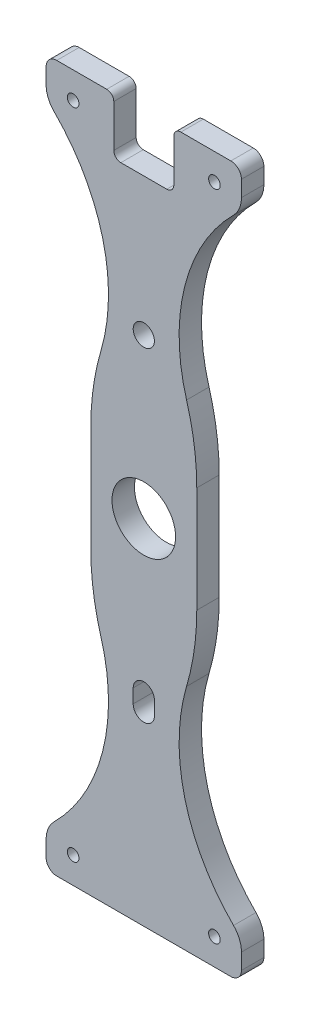
SolidWorks part; units mm, degrees
material "6061-T6 (SS)"
ref_plane "Front Plane" through (0, 0, 0) normal (0, 0, 1) x (1, 0, 0)
ref_plane "Top Plane" through (0, 0, 0) normal (0, 1, 0) x (1, 0, 0)
ref_plane "Right Plane" through (0, 0, 0) normal (1, 0, 0) x (0, 0, -1)
sketch "Sketch1" plane through (0, 0, 0) normal (0, 0, 1) x (1, 0, 0)
  line L5 (-15, 0) -> (15, 0) construction
  line L6 (0, -43.0352) -> (0, -46.957) construction
  line L10 (3, -43.0352) -> (3, -46.957)
  line L13 (240, 100) -> (240, -100) construction
  line L14 (-3, -43.0352) -> (-3, -46.957)
  line L15 (-15, 15) -> (-15, -15)
  line L18 (-24.65, -100) -> (24.65, -100)
  line L21 (15, -15) -> (15, 15)
  line L23 (27.65, 92.5) -> (27.65, 97)
  line L24 (24.65, 100) -> (-24.65, 100)
  line L25 (-27.65, 97) -> (-27.65, 92.5)
  line L27 (27.65, -92.5) -> (27.65, -97)
  line L28 (-27.65, -97) -> (-27.65, -92.5)
  line L29 (-3.92, 79.4898) -> (-3.92, -120.5102) construction
  line L30 (0, 100) -> (0, 0) construction
  line L31 (-10, -49.8891) -> (-10, -92.5) construction
  line L32 (-10, -92.5) -> (10, -92.5) construction
  line L33 (10, -92.5) -> (10, -49.8891) construction
  line L34 (25.4094, 87.0906) -> (0, 61.6813) construction
  circle A0 centre (0, 0) radius 9
  circle A13 centre (0, 44.9961) radius 4.9609 construction
  circle A14 centre (0, -44.9961) radius 4.9609 construction
  circle A18 centre (0, 44.9961) radius 3
  arc A19 (3, -43.0352) -> (-3, -43.0352) centre (0, -43.0352) ccw
  arc A20 (-3, -46.957) -> (3, -46.957) centre (0, -46.957) ccw
  circle A21 centre (20, 92.5) radius 1.65
  circle A22 centre (-20, 92.5) radius 1.65
  circle A23 centre (-20, -92.5) radius 1.65
  circle A24 centre (20, -92.5) radius 1.65
  arc A25 (-27.65, 92.5) -> (-25.4094, 87.0906) centre (-20, 92.5) ccw
  arc A27 (27.65, 92.5) -> (25.4094, 87.0906) centre (20, 92.5) cw
  arc A29 (27.65, -92.5) -> (25.4094, -87.0906) centre (20, -92.5) ccw
  arc A32 (-27.65, -92.5) -> (-25.4094, -87.0906) centre (-20, -92.5) cw
  arc A33 (15, -15) -> (12.1176, -35.1132) centre (-56.6143, -15) cw
  arc A34 (12.1176, -35.1132) -> (25.4094, -87.0906) centre (62.6109, -49.8891) ccw
  arc A35 (-12.1176, -35.1132) -> (-25.4094, -87.0906) centre (-62.6109, -49.8891) cw
  arc A36 (-15, -15) -> (-12.1176, -35.1132) centre (56.6143, -15) ccw
  arc A37 (-15, 15) -> (-12.1176, 35.1132) centre (56.6143, 15) cw
  arc A38 (-12.1176, 35.1132) -> (-25.4094, 87.0906) centre (-62.6109, 49.8891) ccw
  arc A39 (12.1176, 35.1132) -> (25.4094, 87.0906) centre (62.6109, 49.8891) cw
  arc A40 (15, 15) -> (12.1176, 35.1132) centre (-56.6143, 15) ccw
  arc A42 (-24.65, 100) -> (-27.65, 97) centre (-24.65, 97) ccw
  arc A43 (27.65, 97) -> (24.65, 100) centre (24.65, 97) ccw
  arc A44 (-27.65, -97) -> (-24.65, -100) centre (-24.65, -97) ccw
  arc A45 (27.65, -97) -> (24.65, -100) centre (24.65, -97) cw
  point P6 (0, -44.9961)
  point P64 (0, -92.5)
  point P69 (-27.65, 100)
  point P72 (27.65, 100)
  point P75 (-27.65, -100)
  point P78 (27.65, -100)
  dimension "D1" = 18
  dimension "D9" = 9.9219
  dimension "D2" = 6
  dimension "D3" = 3.3
  dimension "D11" = 3
  dimension "D8" = 89.9922
  dimension "D4" = 220
  dimension "D6" = 185
  dimension "D7" = 200
  dimension "D10" = 6
  dimension "D5" = 40
  dimension "D13" = 30
  dimension "D14" = 20
  dimension "D15" = 30
  dimension "D16" = 45
extrude "Boss-Extrude1" add sketch "Sketch1" along normal blind 6.35
sketch "Sketch2" plane through (0, 0, 0) normal (0, 0, -1) x (-1, 0, 0)
  line L0 (-16.1644, 74.6) -> (16.1644, 74.6)
  line L1 (-24.65, 100) -> (24.65, 100) construction
  line L2 (55, 0) -> (-55, 0) construction
  line L3 (-16.1644, -74.6) -> (16.1644, -74.6)
  arc A0 (25.4094, 87.0906) -> (12.1176, 35.1132) centre (62.6109, 49.8891) ccw construction
  arc A1 (-12.1176, 35.1132) -> (-25.4094, 87.0906) centre (-62.6109, 49.8891) ccw construction
  dimension "D1" = 25.4
split line "Split Line1"
sketch "Sketch3" plane through (0, 0, 6.35) normal (0, 0, 1) x (1, 0, 0)
  line L0 (24.65, 100) -> (-24.65, 100) construction
  line L1 (-7.5, 100) -> (7.5, 100) construction
  line L2 (-7.5, 100) -> (-7.5, 85) construction
  line L3 (-7.5, 85) -> (7.5, 85) construction
  line L4 (7.5, 100) -> (7.5, 85) construction
  line L5 (-8.5, 101) -> (-8.5, 86)
  line L6 (-6.5, 84) -> (6.5, 84)
  line L7 (8.5, 101) -> (8.5, 86)
  line L9 (-8.5, 101) -> (8.5, 101) construction
  line L10 (-8.5, 84) -> (8.5, 84) construction
  line L11 (8.5, 101) -> (8.5, 84) construction
  line L12 (-8.5, 101) -> (-8.5, 84) construction
  line L13 (-8.5, 101) -> (8.5, 101)
  arc A0 (6.5, 84) -> (8.5, 86) centre (6.5, 86) ccw
  arc A1 (-8.5, 86) -> (-6.5, 84) centre (-6.5, 86) ccw
  point P6 (0, 100)
  dimension "D3" = 2
  dimension "D1" = 15
  dimension "D2" = 1
extrude "Cut-Extrude1" cut sketch "Sketch3" against normal blind 10
fillet "Fillet1" radius 2 2 edges at (8.5, 100, 3.175) (-8.5, 100, 3.175)
equation "\"frame inside height\"= 200mm'`"
equation "\"hole spacing\"= 20mm"
equation "\"top hole to bottom hole\"= \"frame inside height\" - 7.5mm * 2"
equation "\"D6@Sketch1\"=\"top hole to bottom hole\""
equation "\"D7@Sketch1\"=\"frame inside height\""
equation "\"D5@Sketch1\"=\"hole spacing\"*2"
